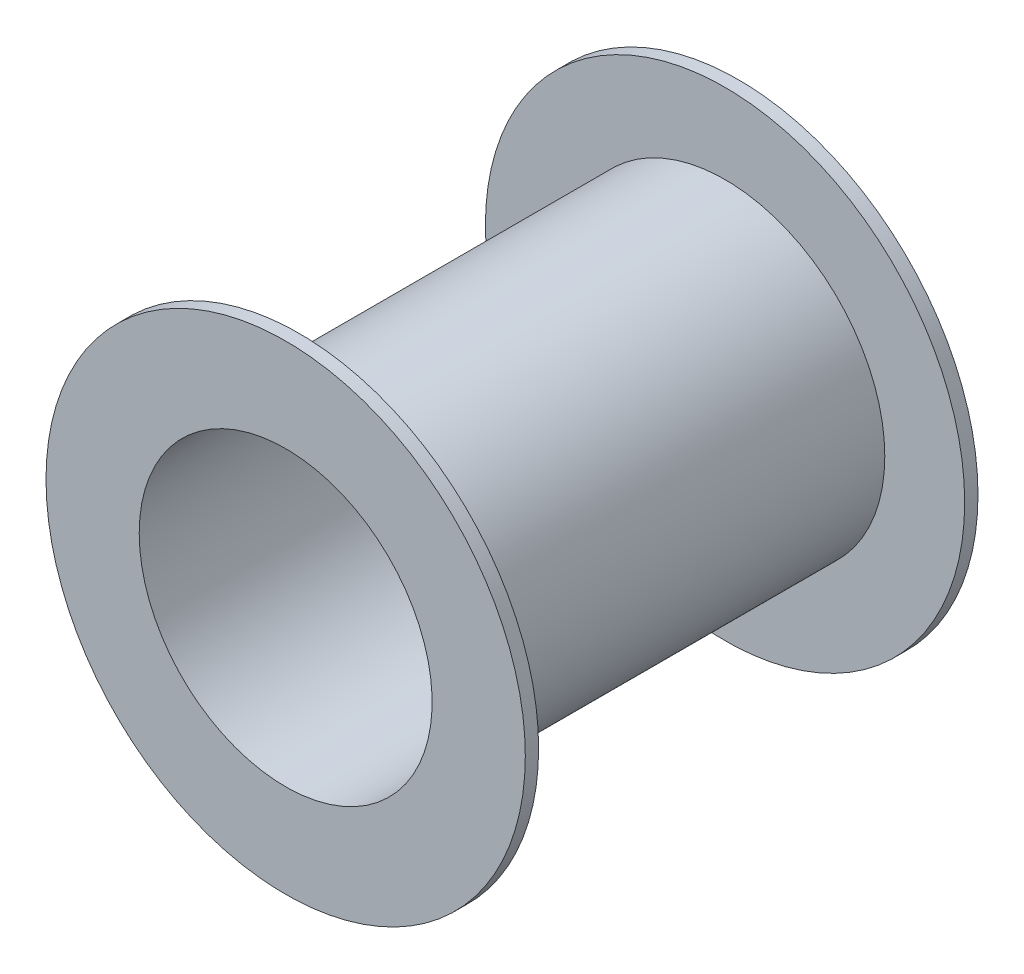
SolidWorks part; units mm, degrees
ref_plane "Front Plane" through (0, 0, 0) normal (0, 0, 1) x (1, 0, 0)
ref_plane "Top Plane" through (0, 0, 0) normal (0, 1, 0) x (1, 0, 0)
ref_plane "Right Plane" through (0, 0, 0) normal (1, 0, 0) x (0, 0, -1)
sketch "Sketch1" plane through (0, 0, 0) normal (0, 1, 0) x (1, 0, 0)
  line L0 (-0.55, 0.85) -> (-0.9, 0.85)
  line L1 (-0.9, 0.85) -> (-0.9, 0.8)
  line L2 (-0.9, 0.8) -> (-0.6, 0.8)
  line L3 (-0.6, 0.8) -> (-0.6, -0.8)
  line L4 (-0.6, -0.8) -> (-0.9, -0.8)
  line L5 (-0.9, -0.8) -> (-0.9, -0.85)
  line L6 (-0.9, -0.85) -> (-0.55, -0.85)
  line L7 (0, 0) -> (0, -1143.6813) construction
  line L8 (-0.55, 0.85) -> (-0.55, -0.85)
  point P2 (-0.0727, -0.2351)
  point P8 (-0.55, 0)
  dimension "D1" = 0.05
  dimension "D2" = 0.6
  dimension "D3" = 0.9
  dimension "D4" = 0.05
  dimension "D5" = 1.6
revolve "Revolve1" add sketch "Sketch1" angle 360 about L7
